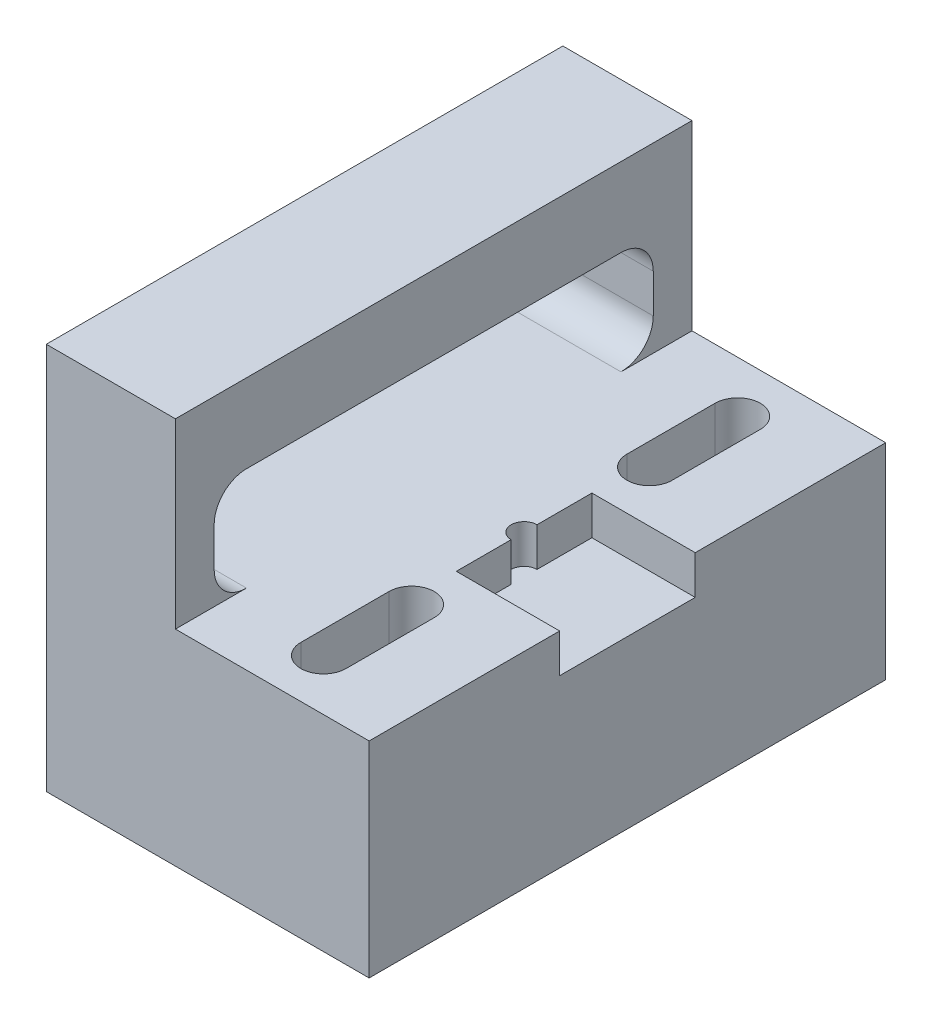
SolidWorks part; units mm, degrees
ref_plane "Front Plane" through (0, 0, 0) normal (0, 0, 1) x (1, 0, 0)
ref_plane "Top Plane" through (0, 0, 0) normal (0, 1, 0) x (1, 0, 0)
ref_plane "Right Plane" through (0, 0, 0) normal (1, 0, 0) x (0, 0, -1)
sketch "Sketch1" plane through (0, 0, 0) normal (1, 0, 0) x (0, 0, -1)
  line L1 (-16.4301, 8.0215) -> (23.5699, 8.0215)
  line L2 (-16.4301, 8.0215) -> (-16.4301, -21.9785)
  line L3 (-16.4301, -21.9785) -> (23.5699, -21.9785)
  line L4 (23.5699, 8.0215) -> (23.5699, -21.9785)
  dimension "D1" = 30
  dimension "D2" = 40
extrude "Boss-Extrude1" add sketch "Sketch1" along normal blind 10
sketch "Sketch2" plane through (0, 0, 0) normal (-1, 0, 0) x (0, 0, 1)
  line L1 (-5.3199, 2.4192) -> (-1.8199, 2.4192)
  line L2 (-5.8199, 1.9192) -> (-5.8199, -6.0808)
  line L3 (-5.3199, -6.5808) -> (-1.8199, -6.5808)
  line L4 (-1.3199, 1.9192) -> (-1.3199, -6.0808)
  line L5 (-23.5699, 8.0215) -> (16.4301, 8.0215) construction
  line L6 (-5.8199, 1.9192) -> (-1.3199, 1.9192)
  line L7 (-1.3199, -6.0808) -> (-5.8199, -6.0808)
  arc A0 (-5.8199, -6.0808) -> (-5.3199, -6.5808) centre (-5.3199, -6.0808) ccw
  arc A1 (-1.8199, -6.5808) -> (-1.3199, -6.0808) centre (-1.8199, -6.0808) ccw
  arc A2 (-1.8199, 2.4192) -> (-1.3199, 1.9192) centre (-1.8199, 1.9192) cw
  arc A3 (-5.3199, 2.4192) -> (-5.8199, 1.9192) centre (-5.3199, 1.9192) ccw
  arc A4 (-2.5699, 2.4192) -> (-4.5699, 2.4192) centre (-3.5699, 2.4192) ccw
  arc A5 (-2.5699, -6.5808) -> (-4.5699, -6.5808) centre (-3.5699, -6.5808) cw
  point P8 (-3.5699, 2.4192)
  point P11 (-3.5699, 8.0215)
  point P16 (-1.3199, -6.5808)
  point P19 (-1.3199, 2.4192)
  point P22 (-5.8199, 2.4192)
  dimension "D5" = 0.5
  dimension "D6" = 1
  dimension "D7" = 1
  dimension "D2" = 0
  dimension "D3" = 4.5
  dimension "D4" = 9
extrude "Cut-Extrude1" cut sketch "Sketch2" against normal blind 1 contours L1 A3 L6 A2 | L3 A1 L7 A0 | L7 L4 L6 L2 | L1 A4 | A5 L3
sketch "Sketch3" plane through (0, 0, 0) normal (-1, 0, 0) x (0, 0, 1)
  line L1 (-18.0699, 1.9192) -> (10.9301, 1.9192)
  line L2 (-20.5699, -0.5808) -> (-20.5699, -3.5808)
  line L3 (-18.0699, -6.0808) -> (10.9301, -6.0808)
  line L4 (13.4301, -0.5808) -> (13.4301, -3.5808)
  line L5 (16.4301, 8.0215) -> (16.4301, -21.9785) construction
  line L7 (-23.5699, 8.0215) -> (16.4301, 8.0215) construction
  arc A0 (-20.5699, -3.5808) -> (-18.0699, -6.0808) centre (-18.0699, -3.5808) ccw
  arc A1 (10.9301, -6.0808) -> (13.4301, -3.5808) centre (10.9301, -3.5808) ccw
  arc A2 (10.9301, 1.9192) -> (13.4301, -0.5808) centre (10.9301, -0.5808) cw
  arc A3 (-18.0699, 1.9192) -> (-20.5699, -0.5808) centre (-18.0699, -0.5808) ccw
  point P6 (-3.5699, 1.9192)
  point P7 (-3.5699, 8.0215)
  dimension "D5" = 2.5
  dimension "D1" = 0
  dimension "D2" = 0
  dimension "D3" = 0
  dimension "D4" = 3
extrude "Cut-Extrude2" cut sketch "Sketch3" against normal through all
sketch "Sketch4" plane through (10, 0, 0) normal (1, 0, 0) x (0, 0, -1)
  line L0 (-16.4301, 8.0215) -> (-16.4301, -21.9785) construction
  line L1 (-16.4301, -6.0808) -> (23.5699, -6.0808)
  line L2 (-16.4301, -6.0808) -> (-16.4301, -21.9785)
  line L3 (-16.4301, -21.9785) -> (23.5699, -21.9785)
  line L4 (23.5699, -6.0808) -> (23.5699, -21.9785)
extrude "Boss-Extrude3" add sketch "Sketch4" along normal blind 15
sketch "Sketch6" plane through (0, -6.0808, 0) normal (0, 1, 0) x (1, 0, 0)
  line L0 (25, 23.5699) -> (25, -16.4301) construction
  line L1 (17, -1.6801) -> (25, -1.6801)
  line L2 (17, -1.6801) -> (17, 8.8199)
  line L3 (17, 8.8199) -> (25, 8.8199)
  line L4 (25, -1.6801) -> (25, 8.8199)
  arc A0 (17, 2.5699) -> (17, 4.5699) centre (17, 3.5699) cw
  point P6 (25, 3.5699)
  point P7 (25, 3.5699)
  line M9 (25, -16.4301) -> (25, 23.5699)
  dimension "D4" = 1
  dimension "D1" = 0
  dimension "D2" = 10.5
  dimension "D3" = 8
extrude "[fix distances] convex_lens_seat" cut sketch "Sketch6" against normal blind 3 contours L3 L2 L1 M9 | A0 L2
sketch "Sketch7" plane through (0, -6.0808, 0) normal (0, 1, 0) x (1, 0, 0)
  line L0 (25, 3.5699) -> (0, 3.5699)
  line L2 (0, 23.5699) -> (0, -16.4301) construction
  line L3 (17.5, -5.642) -> (17.5, -12.4682) construction
  line L4 (25, 23.5699) -> (25, 8.8199) construction
  line L5 (17.5, 12.7818) -> (17.5, 19.608) construction
  line L6 (15.7467, 12.7818) -> (15.7467, 19.608)
  line L7 (19.2533, 12.7818) -> (19.2533, 19.608)
  line L8 (15.7467, -5.642) -> (15.7467, -12.4682)
  line L9 (19.2533, -5.642) -> (19.2533, -12.4682)
  arc A0 (15.7467, 12.7818) -> (19.2533, 12.7818) centre (17.5, 12.7818) ccw
  arc A1 (19.2533, 19.608) -> (15.7467, 19.608) centre (17.5, 19.608) ccw
  arc A2 (15.7467, -5.642) -> (19.2533, -5.642) centre (17.5, -5.642) cw
  arc A3 (19.2533, -12.4682) -> (15.7467, -12.4682) centre (17.5, -12.4682) cw
  point P6 (17.5, 16.1949)
  point P9 (25, 16.1949)
  point P12 (17.5, 16.1949)
  point P17 (0, 0)
  point P20 (17.5, -9.0551)
  dimension "D1" = 0
  dimension "D2" = 3.5066
extrude "[choose screw size, use tight tolerance clearance diameter ] slots" cut sketch "Sketch7" against normal through all contours A1 L6 A0 L7 | A2 L9 A3 L8
